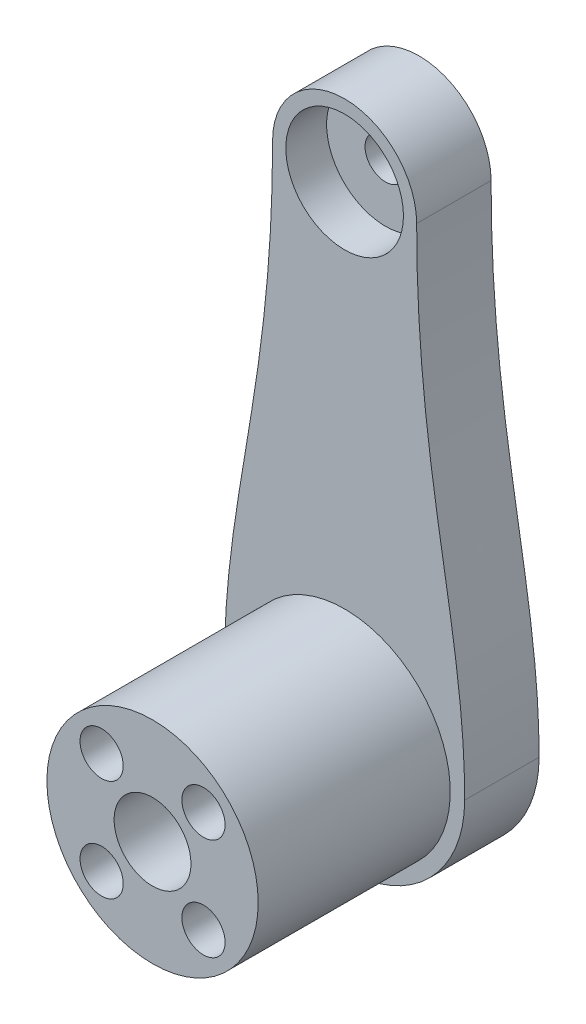
SolidWorks part; units mm, degrees
ref_plane "Front Plane" through (0, 0, 0) normal (0, 0, 1) x (1, 0, 0)
ref_plane "Top Plane" through (0, 0, 0) normal (0, 1, 0) x (1, 0, 0)
ref_plane "Right Plane" through (0, 0, 0) normal (1, 0, 0) x (0, 0, -1)
sketch "Sketch1" plane through (0, 0, 0) normal (0, 0, 1) x (1, 0, 0)
  line L0 (0, 0) -> (0, 49.5) construction
  arc A0 (-12.5, 0) -> (12.5, 0) centre (0, 0) ccw
  arc A1 (7.5, 49.5) -> (-7.5, 49.5) centre (0, 49.5) ccw
  spline S0 degree 3 poles (-7.5, 49.5) (-7.5, 26.6683) (-12.5, 15.6315) (-12.5, 0) knots 0 0 0 0 1 1 1 1
  spline S1 degree 3 poles (7.5, 49.5) (7.5, 26.6683) (12.5, 15.6315) (12.5, 0) knots 0 0 0 0 1 1 1 1
  dimension "D1" = 25
  dimension "D3" = 7.5
  dimension "D2" = 49.5
extrude "Boss-Extrude1" add sketch "Sketch1" along normal blind 7.75 contours A1 S0 A0 S1
sketch "Sketch2" plane through (0, 0, 7.75) normal (0, 0, 1) x (1, 0, 0)
  line L0 (0, 57) -> (0, 49.5) construction
  arc A0 (7.5, 49.5) -> (-7.5, 49.5) centre (0, 49.5) ccw construction
  circle A1 centre (0, 49.5) radius 6.125
  dimension "D1" = 12.25
extrude "Cut-Extrude1" cut sketch "Sketch2" against normal blind 4.25
sketch "Sketch3" plane through (0, 0, 3.5) normal (0, 0, 1) x (1, 0, 0)
  circle A0 centre (0, 49.5) radius 2.125
  dimension "D1" = 4.25
extrude "Cut-Extrude2" cut sketch "Sketch3" against normal up to next
sketch "Sketch4" plane through (0, 0, 7.75) normal (0, 0, 1) x (1, 0, 0)
  circle A0 centre (0, 0) radius 11
  dimension "D1" = 22
extrude "Boss-Extrude2" add sketch "Sketch4" along normal blind 20
sketch "Sketch5" plane through (0, 0, 27.75) normal (0, 0, 1) x (1, 0, 0)
  line L0 (0, 0) -> (0, 10) construction
  line L1 (0, 0) -> (10, 0) construction
  line L2 (0, 0) -> (10.6066, 10.6066) construction
  circle A1 centre (5.3033, 5.3033) radius 2.25
  circle A7 centre (5.3033, -5.3033) radius 2.25
  circle A15 centre (-5.3033, -5.3033) radius 2.25
  circle A16 centre (-5.3033, 5.3033) radius 2.25
  circle A17 centre (0, 0) radius 4
  point P16 (0, 0)
  point P17 (0, 0)
  point P23 (0, 0)
  dimension "D1" = 4
  dimension "D2" = 4.5
  dimension "D3" = 15
extrude "Cut-Extrude3" cut sketch "Sketch5" against normal blind 10
sketch "Sketch6" plane through (0, 0, 0) normal (0, 0, -1) x (-1, 0, 0)
  circle A0 centre (0, 0) radius 2.125
  dimension "D1" = 4.25
extrude "Cut-Extrude4" cut sketch "Sketch6" against normal through all
sketch "Sketch7" plane through (0, 0, 0) normal (0, 0, -1) x (-1, 0, 0)
  arc A0 (-12.5, 0) -> (12.5, 0) centre (0, 0) ccw construction
  point P0 (0, -12.5)
ref_plane "Plane1" through (0, -12.5, 0) normal (0, 1, 0) x (1, 0, 0)
sketch "Sketch8" plane through (0, 0, 0) normal (0, 0, -1) x (-1, 0, 0)
  circle A0 centre (0, 0) radius 6.125
  dimension "D1" = 12.25
sketch "Sketch9" plane through (0, 0, 0) normal (0, 0, -1) x (-1, 0, 0)
  line L0 (0, -12.5) -> (0, 47.5) construction
  line L1 (0, -12.5) -> (0, 37.5) construction
  line L2 (0, 37.5) -> (0, 47.5) construction
  line L3 (0, 51.5) -> (0, 57) construction
  line L4 (0, 51.5) -> (0, 57) construction
  line L5 (0, 37.5) -> (0, 49.5) construction
  arc A0 (7.5, 49.5) -> (-7.5, 49.5) centre (0, 49.5) ccw construction
  circle A1 centre (0, 49.5) radius 2
  dimension "D1" = 69.5
sketch "Sketch10" plane through (0, 0, 0) normal (0, 0, -1) x (-1, 0, 0)
  circle A0 centre (0, 0) radius 2.75
  dimension "D1" = 5.5
extrude "Cut-Extrude5" cut sketch "Sketch10" against normal blind 6
